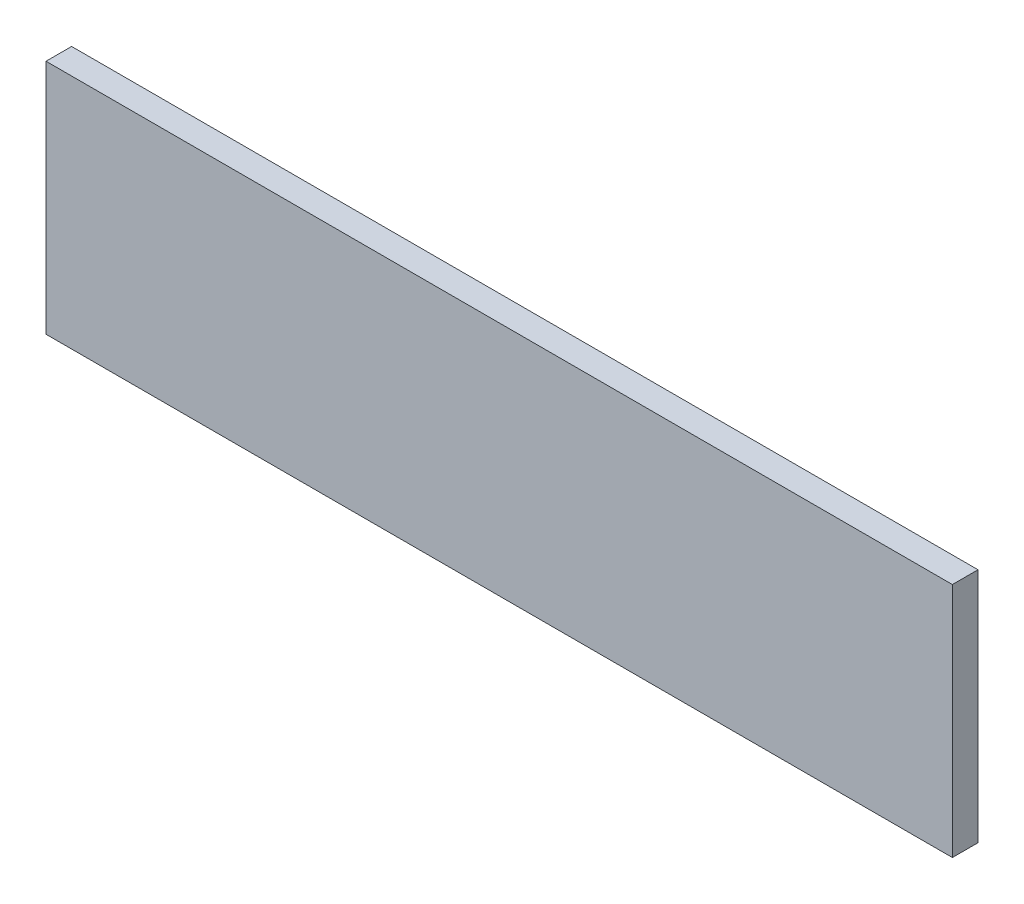
SolidWorks part; units mm, degrees
ref_plane "Front Plane" through (0, 0, 0) normal (0, 0, 1) x (1, 0, 0)
ref_plane "Top Plane" through (0, 0, 0) normal (0, 1, 0) x (1, 0, 0)
ref_plane "Right Plane" through (0, 0, 0) normal (1, 0, 0) x (0, 0, -1)
sketch "Sketch1" plane through (0, 0, 0) normal (0, 0, 1) x (1, 0, 0)
  line L1 (-29.21, -7.62) -> (29.21, -7.62)
  line L2 (-29.21, -7.62) -> (-29.21, 7.62)
  line L3 (-29.21, 7.62) -> (29.21, 7.62)
  line L4 (29.21, -7.62) -> (29.21, 7.62)
  line L5 (-29.21, -7.62) -> (29.21, 7.62) construction
  line L6 (-29.21, 7.62) -> (29.21, -7.62) construction
  point P0 (0, 0)
  dimension "D1" = 15.24
  dimension "D2" = 58.42
extrude "Boss-Extrude1" add sketch "Sketch1" along normal blind 1.651 contours L2 L3 L4 L1
